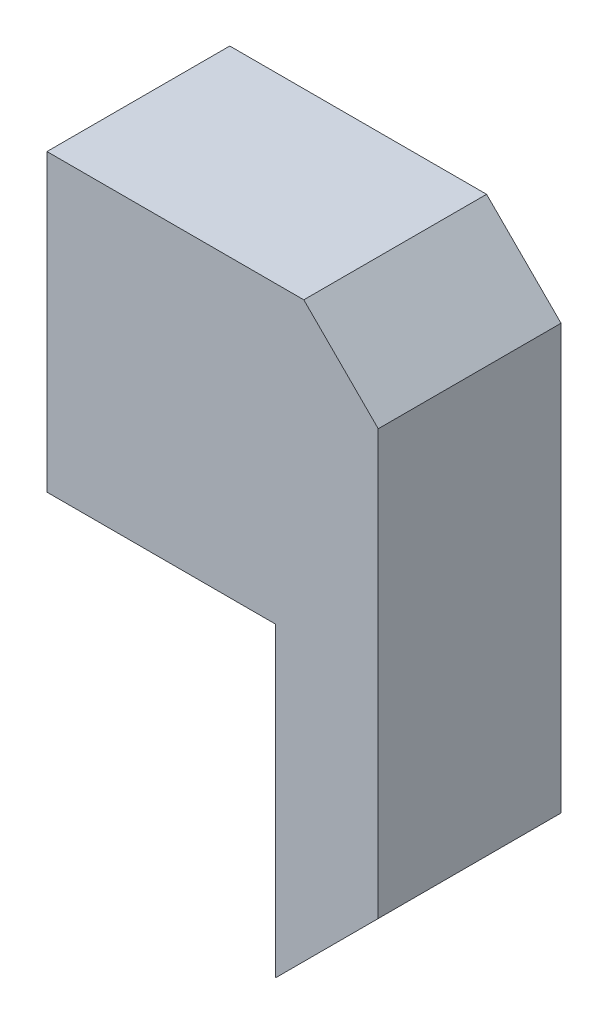
SolidWorks part; units mm, degrees
ref_plane "Front Plane" through (0, 0, 0) normal (0, 0, 1) x (1, 0, 0)
ref_plane "Top Plane" through (0, 0, 0) normal (0, 1, 0) x (1, 0, 0)
ref_plane "Right Plane" through (0, 0, 0) normal (1, 0, 0) x (0, 0, -1)
sketch "Sketch1" plane through (0, 0, 0) normal (0, 0, 1) x (1, 0, 0)
  line L0 (0, 0) -> (0, 404.8125)
  line L1 (0, 404.8125) -> (352.425, 404.8125)
  line L2 (352.425, 404.8125) -> (454.5754, 302.6621)
  line L3 (454.5754, 302.6621) -> (454.5754, -279.4)
  line L4 (454.5754, -279.4) -> (313.2879, -420.6875)
  line L5 (313.2879, -420.6875) -> (313.2879, 0)
  line L6 (313.2879, 0) -> (0, 0)
  dimension "D1" = 404.8125
  dimension "D2" = 352.425
  dimension "D3" = 141.2875
  dimension "D4" = 420.6875
  dimension "D5" = 135
  dimension "D6" = 135
  dimension "D7" = 144.4625
extrude "Boss-Extrude1" add sketch "Sketch1" against normal blind 250.825
shell "Shell1" thickness 1.5875
